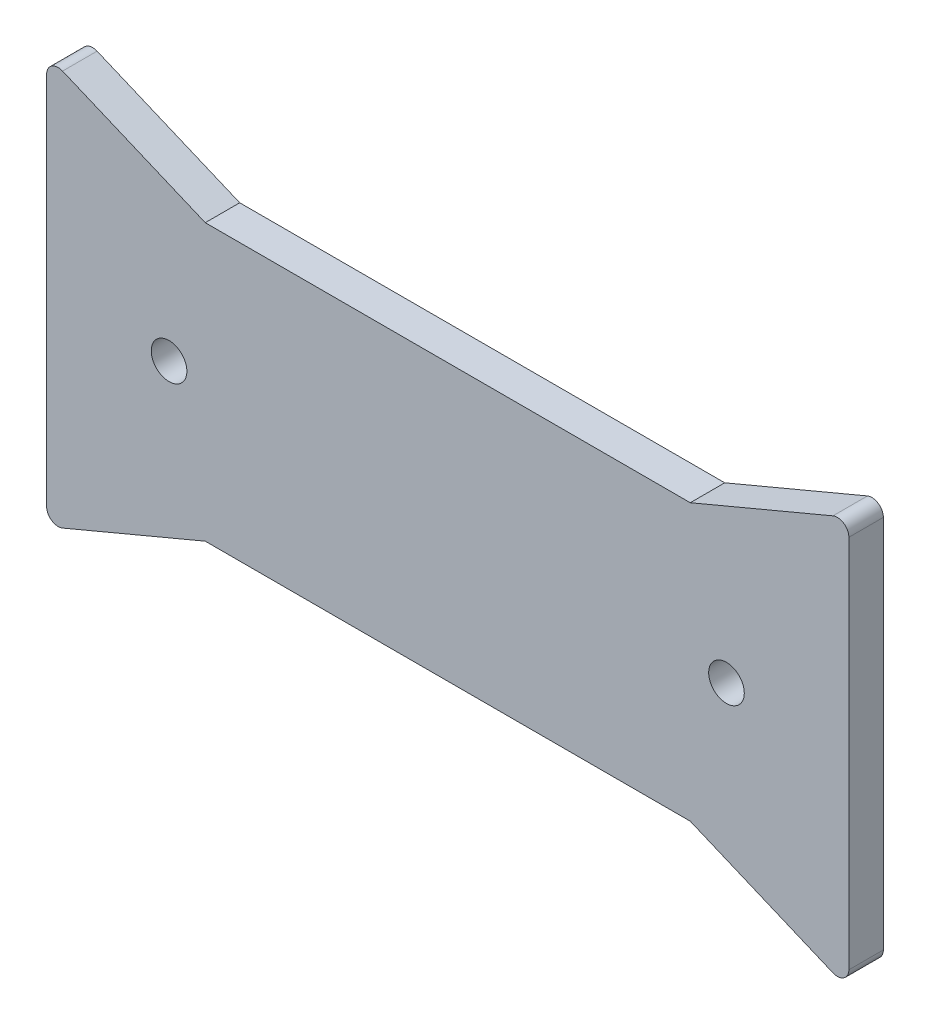
SolidWorks part; units mm, degrees
ref_plane "Спереди" through (0, 0, 0) normal (0, 0, 1) x (1, 0, 0)
ref_plane "Сверху" through (0, 0, 0) normal (0, 1, 0) x (1, 0, 0)
ref_plane "Справа" through (0, 0, 0) normal (1, 0, 0) x (0, 0, -1)
sketch "Эскиз1" plane through (0, 0, 0) normal (0, 0, 1) x (1, 0, 0)
  line L0 (55, 0) -> (-55, 0) construction
  line L2 (34.9, -12) -> (34.9, 12)
  line L4 (-34.9, -12) -> (-34.9, 12)
  line L5 (34.9, -12) -> (-34.9, 12) construction
  line L6 (34.9, 12) -> (-34.9, -12) construction
  line L15 (0, -55) -> (0, 55) construction
  line L26 (21.1, -12) -> (-21.1, -12)
  line L27 (21.1, 12) -> (-21.1, 12)
  line L32 (-34.9, 12) -> (-34.9, 17.8)
  line L33 (-34.9, 17.8) -> (-21.1, 12)
  line L34 (-34.9, -17.8) -> (-21.1, -12)
  line L35 (-34.9, -12) -> (-34.9, -17.8)
  line L36 (34.9, -12) -> (34.9, -17.8)
  line L37 (34.9, -17.8) -> (21.1, -12)
  line L38 (34.9, 12) -> (34.9, 17.8)
  line L39 (34.9, 17.8) -> (21.1, 12)
  point P0 (0, 0)
  dimension "D1" = 69.8
  dimension "D2" = 24
  dimension "D3" = 5.8
  dimension "D4" = 13.8
  dimension "D5" = 24
extrude "Бобышка-Вытянуть1" add sketch "Эскиз1" along normal blind 3
fillet "Скругление1" radius 1 4 edges at (34.9, 17.8, 1.5) (34.9, -17.8, 1.5) (-34.9, -17.8, 1.5) (-34.9, 17.8, 1.5)
sketch "Эскиз2" plane through (0, 0, 3) normal (0, 0, 1) x (1, 0, 0)
  circle A0 centre (-24.25, 0) radius 1.55
  circle A1 centre (24.25, 0) radius 1.55
  dimension "D1" = 24.25
  dimension "D2" = 24.25
extrude "Вырез-Вытянуть1" cut sketch "Эскиз2" against normal through all
